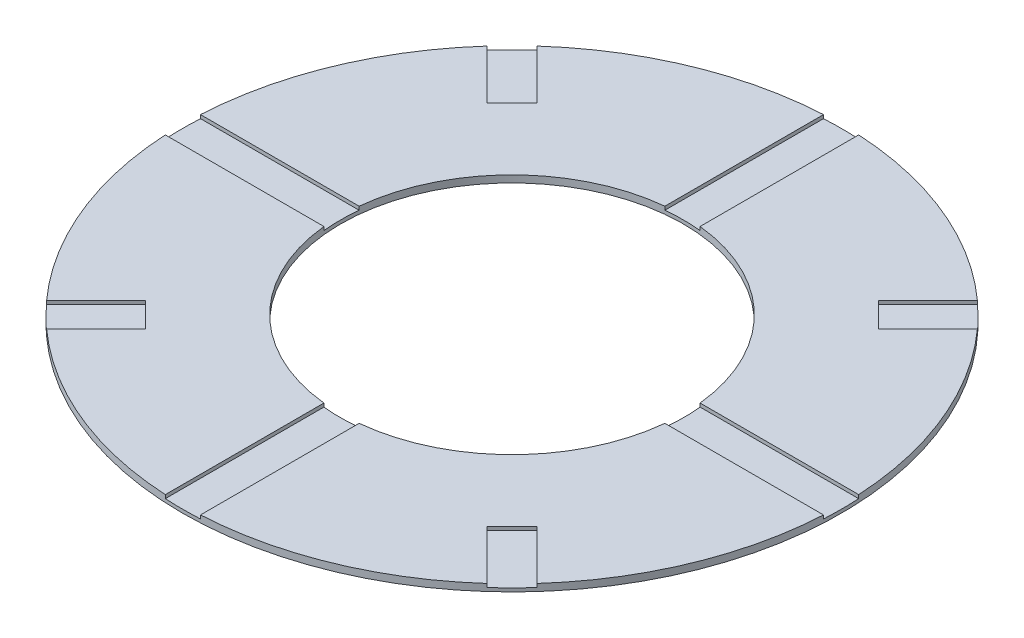
SolidWorks part; units mm, degrees
ref_plane "Front Plane" through (0, 0, 0) normal (0, 0, 1) x (1, 0, 0)
ref_plane "Top Plane" through (0, 0, 0) normal (0, 1, 0) x (1, 0, 0)
ref_plane "Right Plane" through (0, 0, 0) normal (1, 0, 0) x (0, 0, -1)
sketch "Croquis2" plane through (0, 0, 0) normal (0, 1, 0) x (1, 0, 0)
  circle A0 centre (0, 0) radius 9.365
  circle A1 centre (0, 0) radius 4.87
  dimension "D1" = 9.74
  dimension "D2" = 18.73
extrude "Saliente-Extruir1" add sketch "Croquis2" along normal blind 0.2
sketch "Croquis3" plane through (0, 0.2, 0) normal (0, 1, 0) x (1, 0, 0)
  line L0 (-9.365, 0) -> (9.365, 0) construction
  line L1 (0, 9.365) -> (0, -9.365) construction
  line L2 (0, 0) -> (13.2441, 13.2441) construction
  line L3 (-9.365, 0.5) -> (9.365, 0.5)
  line L4 (-9.365, 0.5) -> (-9.365, -0.5)
  line L5 (-9.365, -0.5) -> (9.365, -0.5)
  line L6 (9.365, 0.5) -> (9.365, -0.5)
  line L7 (-0.5, 9.365) -> (0.5, 9.365)
  line L8 (-0.5, 9.365) -> (-0.5, -9.365)
  line L9 (-0.5, -9.365) -> (0.5, -9.365)
  line L10 (0.5, 9.365) -> (0.5, -9.365)
  line L11 (6.2685, 6.9756) -> (6.9756, 6.2685)
  line L12 (6.9756, 6.2685) -> (5.5614, 4.8543)
  line L13 (5.5614, 4.8543) -> (4.8543, 5.5614)
  line L14 (4.8543, 5.5614) -> (6.2685, 6.9756)
  line L15 (5.5614, -4.8543) -> (6.9756, -6.2685)
  line L16 (6.9756, -6.2685) -> (6.2685, -6.9756)
  line L17 (6.2685, -6.9756) -> (4.8543, -5.5614)
  line L18 (4.8543, -5.5614) -> (5.5614, -4.8543)
  line L19 (-4.8543, -5.5614) -> (-6.2685, -6.9756)
  line L20 (-6.2685, -6.9756) -> (-6.9756, -6.2685)
  line L21 (-6.9756, -6.2685) -> (-5.5614, -4.8543)
  line L22 (-5.5614, -4.8543) -> (-4.8543, -5.5614)
  line L23 (-5.5614, 4.8543) -> (-6.9756, 6.2685)
  line L24 (-6.9756, 6.2685) -> (-6.2685, 6.9756)
  line L25 (-6.2685, 6.9756) -> (-4.8543, 5.5614)
  line L26 (-4.8543, 5.5614) -> (-5.5614, 4.8543)
  line L27 (-7.324, 7.324) -> (-5.2078, 5.2078) construction
  circle A0 centre (0, 0) radius 9.365 construction
  point P20 (6.6221, 6.6221)
  point P25 (5.2078, 5.2078)
  point P38 (0.078, 0.6601)
  point P39 (0, 0)
  point P41 (-5.2078, -5.2078)
  circle M1 centre (0, 0) radius 9.365
  circle M2 centre (0, 0) radius 4.87
  dimension "D1" = 1
  dimension "D2" = 1
  dimension "D3" = 45
  dimension "D4" = 1
  dimension "D5" = 2
  dimension "D6" = 4
extrude "Cortar-Extruir1" cut sketch "Croquis3" against normal blind 0.1 contours L10 L8 M1 M2 | L5 L3 M1 M2 | L10 L8 M2 M1 | L5 L3 M2 M1 | L14 L13 L12 M1 | L15 L18 L17 M1 | L19 L22 L21 M1 | L26 L25 L24 L23
